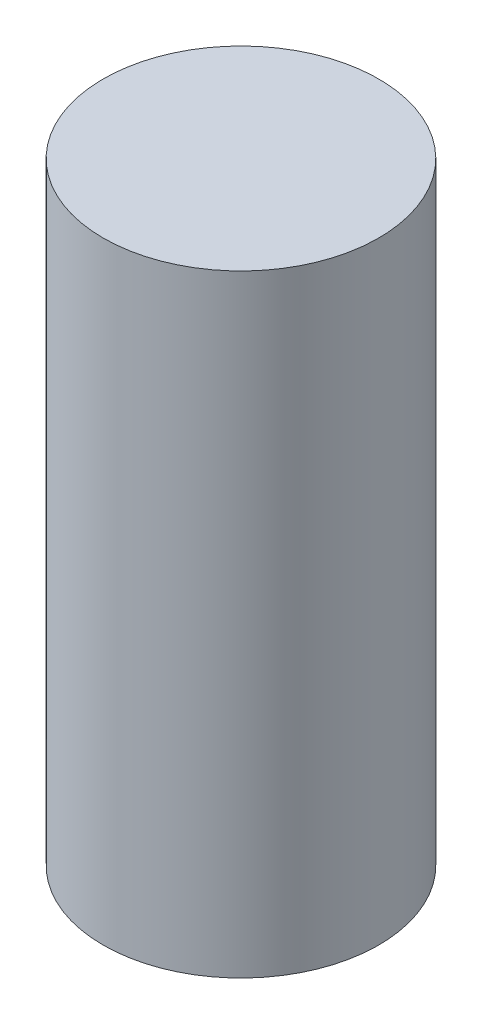
SolidWorks part; units mm, degrees
ref_plane "Front Plane" through (0, 0, 0) normal (0, 0, 1) x (1, 0, 0)
ref_plane "Top Plane" through (0, 0, 0) normal (0, 1, 0) x (1, 0, 0)
ref_plane "Right Plane" through (0, 0, 0) normal (1, 0, 0) x (0, 0, -1)
sketch "Sketch1" plane through (0, 0, 0) normal (1, 0, 0) x (0, 0, -1)
  line L0 (0, 4.4447) -> (0, -12.8914) construction
  line L2 (0, 0) -> (-2.25, 0)
  line L3 (0, 0) -> (0, -10)
  line L4 (0, -10) -> (-2.25, -10)
  line L5 (-2.25, 0) -> (-2.25, -10)
  dimension "D1" = 4.5
  dimension "D2" = 10
revolve "Revolve1" add sketch "Sketch1" angle 360 about L0
